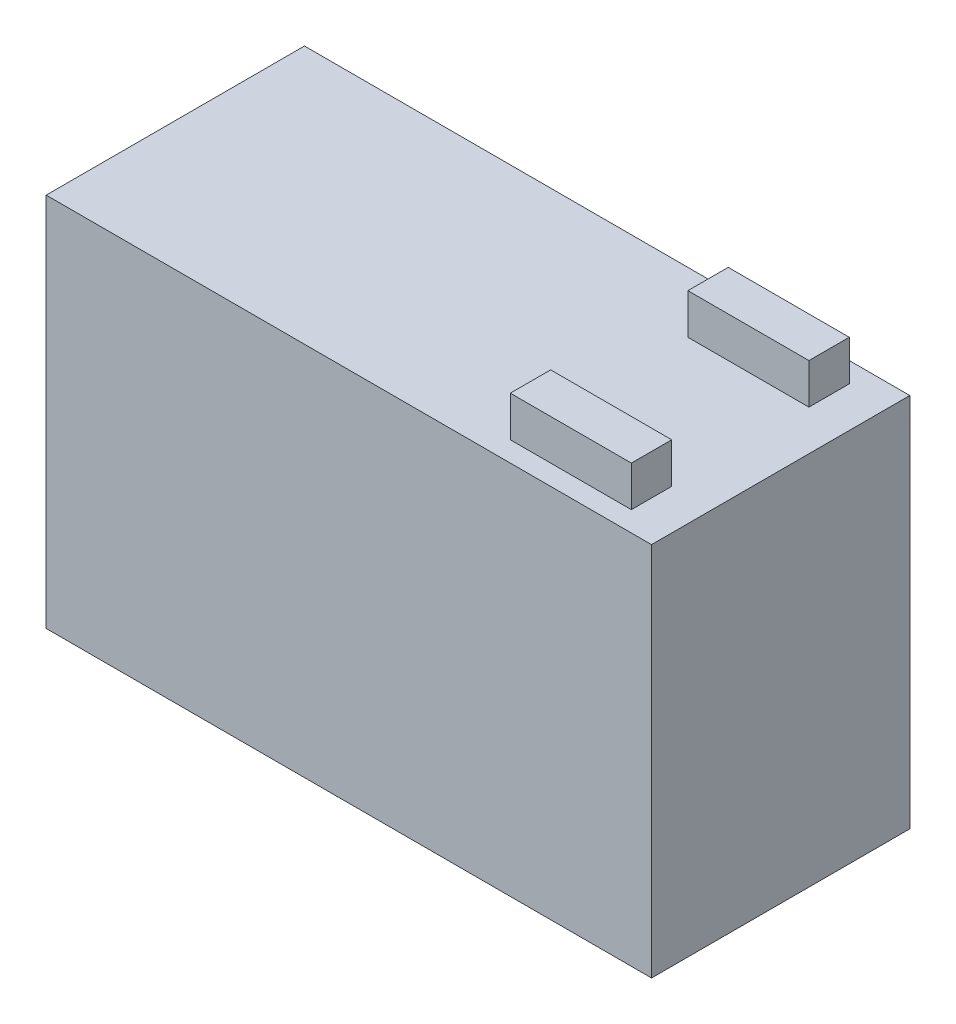
SolidWorks part; units mm, degrees
ref_plane "Plan de face" through (0, 0, 0) normal (0, 0, 1) x (1, 0, 0)
ref_plane "Plan de dessus" through (0, 0, 0) normal (0, 1, 0) x (1, 0, 0)
ref_plane "Plan de droite" through (0, 0, 0) normal (1, 0, 0) x (0, 0, -1)
sketch "Esquisse1" plane through (0, 0, 0) normal (0, 1, 0) x (1, 0, 0)
  line L1 (-34.7309, 32) -> (115.2691, 32)
  line L2 (-34.7309, 32) -> (-34.7309, -32)
  line L3 (-34.7309, -32) -> (115.2691, -32)
  line L4 (115.2691, 32) -> (115.2691, -32)
  dimension "D1" = 150
  dimension "D2" = 64
  dimension "D3" = 32
extrude "Boss.-Extru.1" add sketch "Esquisse1" along normal blind 93
sketch "Esquisse2" plane through (0, 93, 0) normal (0, 1, 0) x (1, 0, 0)
  line L1 (105.2691, -17) -> (75.2691, -17)
  line L2 (105.2691, -17) -> (105.2691, -27)
  line L3 (105.2691, -27) -> (75.2691, -27)
  line L4 (75.2691, -17) -> (75.2691, -27)
  line L5 (-34.7309, -32) -> (115.2691, -32) construction
  line L6 (115.2691, -32) -> (115.2691, 32) construction
  dimension "D1" = 30
  dimension "D2" = 10
  dimension "D3" = 5
  dimension "D4" = 10
extrude "Boss.-Extru.2" add sketch "Esquisse2" along normal blind 10
mirror "Symétrie1" about plane through (0, 0, 0) normal (0, 0, 1) of "Boss.-Extru.2"
